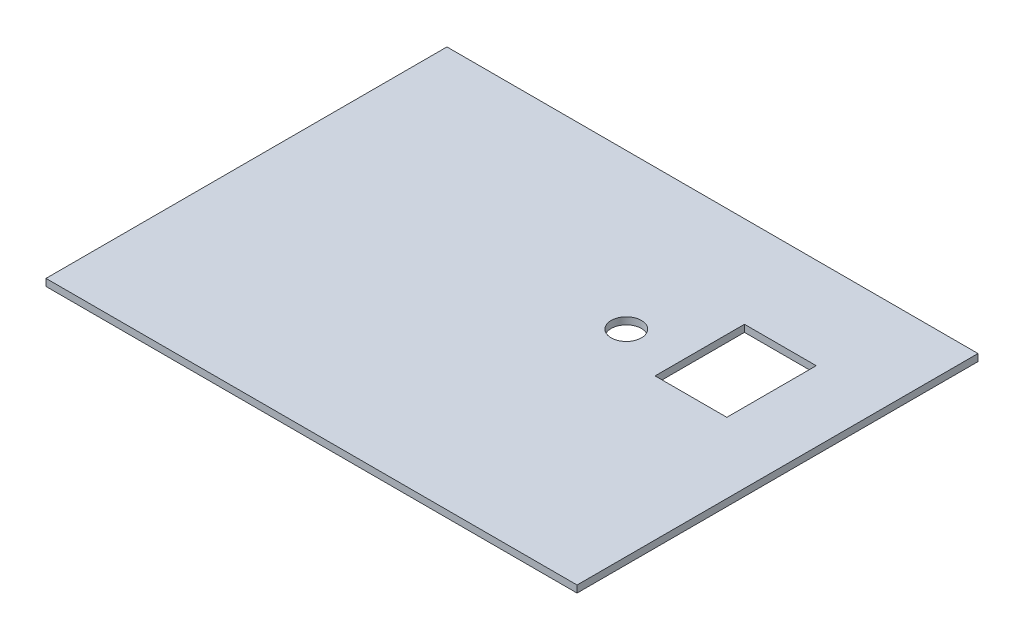
SolidWorks part; units mm, degrees
ref_plane "Front Plane" through (0, 0, 0) normal (0, 0, 1) x (1, 0, 0)
ref_plane "Top Plane" through (0, 0, 0) normal (0, 1, 0) x (1, 0, 0)
ref_plane "Right Plane" through (0, 0, 0) normal (1, 0, 0) x (0, 0, -1)
sketch "Sketch1" plane through (0, 0, 0) normal (0, 1, 0) x (1, 0, 0)
  line L1 (0, 0) -> (191.77, 0)
  line L2 (0, 0) -> (0, 144.78)
  line L3 (0, 144.78) -> (191.77, 144.78)
  line L4 (191.77, 0) -> (191.77, 144.78)
  line L5 (166.37, 111.76) -> (140.462, 111.76)
  line L6 (166.37, 111.76) -> (166.37, 79.4766)
  line L7 (166.37, 79.4766) -> (140.462, 79.4766)
  line L8 (140.462, 111.76) -> (140.462, 79.4766)
  circle A0 centre (120.65, 88.9) radius 5.461
  dimension "D7" = 10.922
  dimension "D8" = 88.9
  dimension "D9" = 71.12
  dimension "D1" = 191.77
  dimension "D2" = 144.78
  dimension "D3" = 32.2834
  dimension "D4" = 25.908
  dimension "D5" = 33.02
  dimension "D6" = 25.4
extrude "Boss-Extrude1" add sketch "Sketch1" along normal blind 2.54
